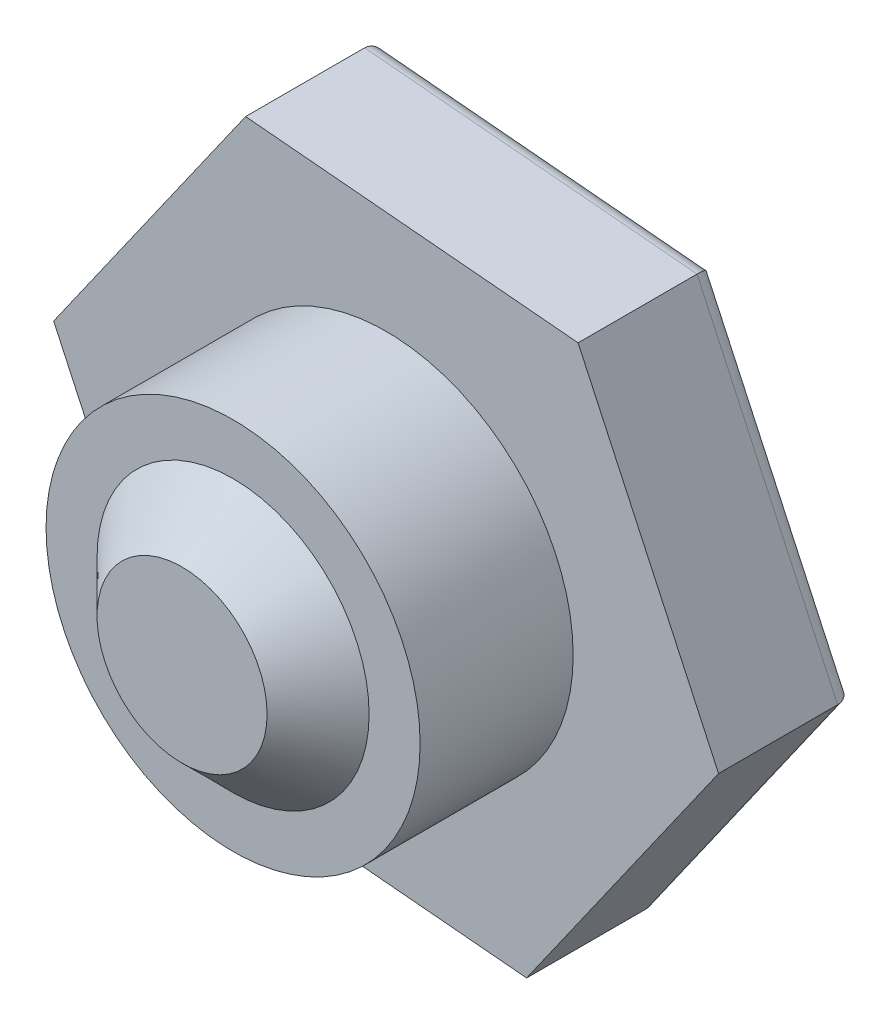
SolidWorks part; units mm, degrees
material "2014-T6"
ref_plane "Piano frontale" through (0, 0, 0) normal (0, 0, 1) x (1, 0, 0)
ref_plane "Piano superiore" through (0, 0, 0) normal (0, 1, 0) x (1, 0, 0)
ref_plane "Piano destro" through (0, 0, 0) normal (1, 0, 0) x (0, 0, -1)
sketch "Schizzo1" plane through (0, 0, 0) normal (0, 0, 1) x (1, 0, 0)
  circle A0 centre (0, 0) radius 11
  dimension "D1" = 22
extrude "Estrusione-Estrusione1" add sketch "Schizzo1" along normal blind 9
cosmetic thread "Filettatura cosmetica1" parameters "D1"=9, "D2"=19.252
sketch "Schizzo2" plane through (0, 0, 0) normal (0, 0, -1) x (-1, 0, 0)
  line L1 (-19.552, -1.7473) -> (-8.2628, -17.8062)
  line L2 (-8.2628, -17.8062) -> (11.2892, -16.0589)
  line L3 (11.2892, -16.0589) -> (19.552, 1.7473)
  line L4 (19.552, 1.7473) -> (8.2628, 17.8062)
  line L5 (8.2628, 17.8062) -> (-11.2892, 16.0589)
  line L6 (-11.2892, 16.0589) -> (-19.552, -1.7473)
  circle A0 centre (0, 0) radius 17 construction
  dimension "D1" = 34
extrude "Estrusione-Estrusione2" add sketch "Schizzo2" along normal blind 8
fillet "Raccordo1" radius 1 6 edges at (1.5132, 16.9325, -8) (-13.9074, 9.7767, -8) (-15.4206, -7.1558, -8) (-1.5132, -16.9325, -8) (13.9074, -9.7767, -8) (15.4206, 7.1558, -8)
ref_plane "Piano1" through (0, 0, 12) normal (0, 0, 1) x (1, 0, 0)
sketch "Schizzo4" plane through (0, 0, 12) normal (0, 0, 1) x (1, 0, 0)
  circle A0 centre (0, 0) radius 5
  dimension "D1" = 10
sketch "Schizzo5" plane through (0, 0, 9) normal (0, 0, 1) x (1, 0, 0)
  circle A0 centre (0, 0) radius 8
  dimension "D1" = 16
loft "Loft1" add profiles "Schizzo5", "Schizzo4"
